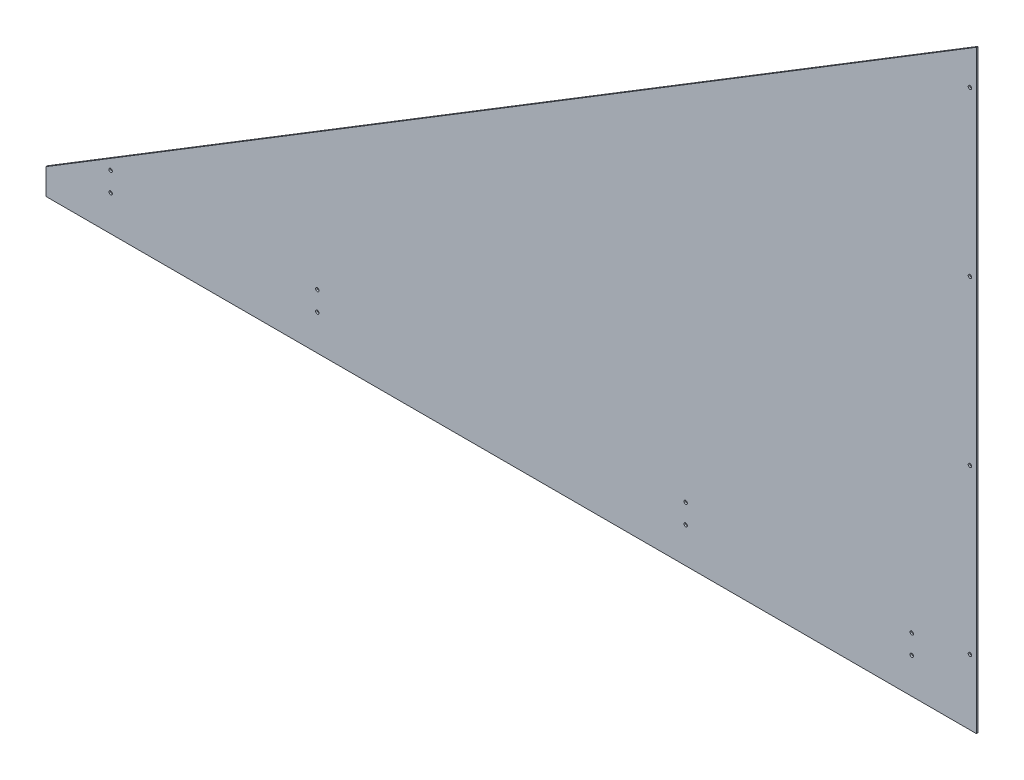
SolidWorks part; units mm, degrees
material "PC High Viscosity"
ref_plane "Front Plane" through (0, 0, 0) normal (0, 0, 1) x (1, 0, 0)
ref_plane "Top Plane" through (0, 0, 0) normal (0, 1, 0) x (1, 0, 0)
ref_plane "Right Plane" through (0, 0, 0) normal (1, 0, 0) x (0, 0, -1)
sketch "Sketch1" plane through (0, 0, 0) normal (0, 0, 1) x (1, 0, 0)
  line L0 (0, 0) -> (1828.8, 1117.6)
  line L5 (1828.8, 1117.6) -> (1828.8, 0)
  line L6 (1828.8, 0) -> (0, 0)
  dimension "D1" = 1828.8
  dimension "D2" = 1117.6
extrude "Boss-Extrude1" add sketch "Sketch1" along normal blind 3.175
hole_wizard "1/4 Clearance Hole1" positions "Sketch2" profile "Sketch3" hole size "1/4" standard "ANSI Inch" end condition through all
sketch "Sketch2" plane through (0, 0, 0) normal (0, 0, -1) x (-1, 0, 0)
  line L0 (0, 0) -> (-1828.8, 0) construction
  line L1 (-1828.8, 0) -> (-1828.8, 1117.6) construction
  point P0 (-1816.1, 77.7875)
  point P7 (-1816.1, 399.5208)
  point P8 (-1816.1, 721.2542)
  point P9 (-1816.1, 1042.9875)
  point P17 (-1701.8, 19.05)
  point P19 (-1701.8, 57.15)
  point P40 (-1257.3, 57.15)
  point P42 (-1257.3, 19.05)
  point P44 (-533.4, 57.15)
  point P46 (-533.4, 19.05)
  point P48 (-127, 57.15)
  point P50 (-127, 19.05)
  dimension "D2" = 77.7875
  dimension "D3" = 74.6125
  dimension "D4" = 12.7
  dimension "D5" = 19.05
  dimension "D6" = 38.1
  dimension "D7" = 127
  dimension "D9" = 127
  dimension "D8" = 444.5
  dimension "D10" = 406.4
  dimension "D1" = 4
sketch "Sketch3" plane through (1816.1, 77.7875, 0) normal (1, 0, 0) x (0, 1, 0)
  line L0 (0, 0) -> (0, 3.175)
  line L1 (0, 3.175) -> (3.3782, 3.175)
  line L2 (3.3782, 3.175) -> (3.3782, 0)
  line L5 (3.3782, 0) -> (0, 0)
  line L11 (0, -6.35) -> (0, 107.95) construction
  dimension "Thru Hole Dia." = 6.7564
  dimension "Thru Hole Depth" = 3.175
sketch "Sketch7" plane through (0, 0, 0) normal (0, 0, -1) x (-1, 0, 0)
  line L1 (-1828.8, 0) -> (0, 0)
  line L2 (-1828.8, 0) -> (-1828.8, -50.8)
  line L3 (-1828.8, -50.8) -> (0, -50.8)
  line L4 (0, 0) -> (0, -50.8)
  dimension "D1" = 50.8
extrude "Boss-Extrude3" add sketch "Sketch7" against normal up to surface (3.175 mm away) up to face at (1812.7218, 77.7875, 3.175)
